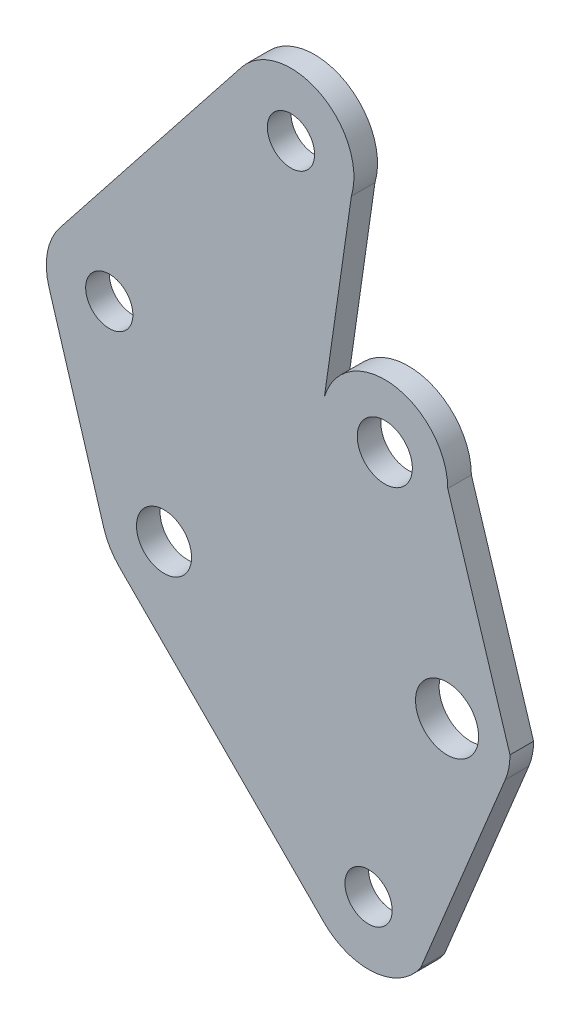
SolidWorks part; units mm, degrees
material "7075-O (SS)"
ref_plane "Front" through (0, 0, 0) normal (0, 0, 1) x (1, 0, 0)
ref_plane "Top" through (0, 0, 0) normal (0, 1, 0) x (1, 0, 0)
ref_plane "Right" through (0, 0, 0) normal (1, 0, 0) x (0, 0, -1)
sketch "草图1" plane through (0, 0, 0) normal (0, 0, 1) x (1, 0, 0)
  line L11 (480.9661, -500.4832) -> (492.5096, -485.8839) construction
  line L31 (494.6058, -527.8392) -> (481.6096, -514.7911)
  line L32 (500.7606, -527.2463) -> (506.1241, -514.2356)
  line L33 (496.3477, -487.0122) -> (494.6352, -498.9096)
  line L34 (502.4728, -500.0378) -> (506.4259, -512.712)
  line L35 (477.8284, -498.0024) -> (489.3715, -483.4028)
  line L36 (480.6153, -513.1275) -> (477.1377, -501.6424)
  circle A19 centre (480.9661, -500.4832) radius 1.5
  circle A21 centre (484.4437, -511.9683) radius 1.75
  circle A27 centre (492.5096, -485.8839) radius 1.5
  circle A34 centre (502.4283, -512.712) radius 2.0039
  circle A35 centre (497.4398, -525.0164) radius 1.5
  circle A36 centre (498.4728, -500.0378) radius 1.75
  circle A37 centre (524.4095, -513.6211) radius 1.5 construction
  arc A43 (496.3477, -487.0122) -> (489.3715, -483.4028) centre (492.5096, -485.8839) ccw
  arc A44 (477.8284, -498.0024) -> (477.1377, -501.6424) centre (480.9661, -500.4832) ccw
  arc A45 (506.1241, -514.2356) -> (506.4259, -512.712) centre (502.4283, -512.712) ccw
  arc A46 (494.6058, -527.8392) -> (500.7606, -527.2463) centre (497.4398, -525.0164) ccw
  arc A47 (502.4728, -500.0378) -> (494.6352, -498.9096) centre (498.4728, -500.0378) ccw
  arc A48 (480.6153, -513.1275) -> (481.6096, -514.7911) centre (484.4437, -511.9683) ccw
  dimension "D1" = 3.5
  dimension "D2" = 3.5
extrude "凸台-拉伸1" add sketch "草图1" along normal blind 1.5
